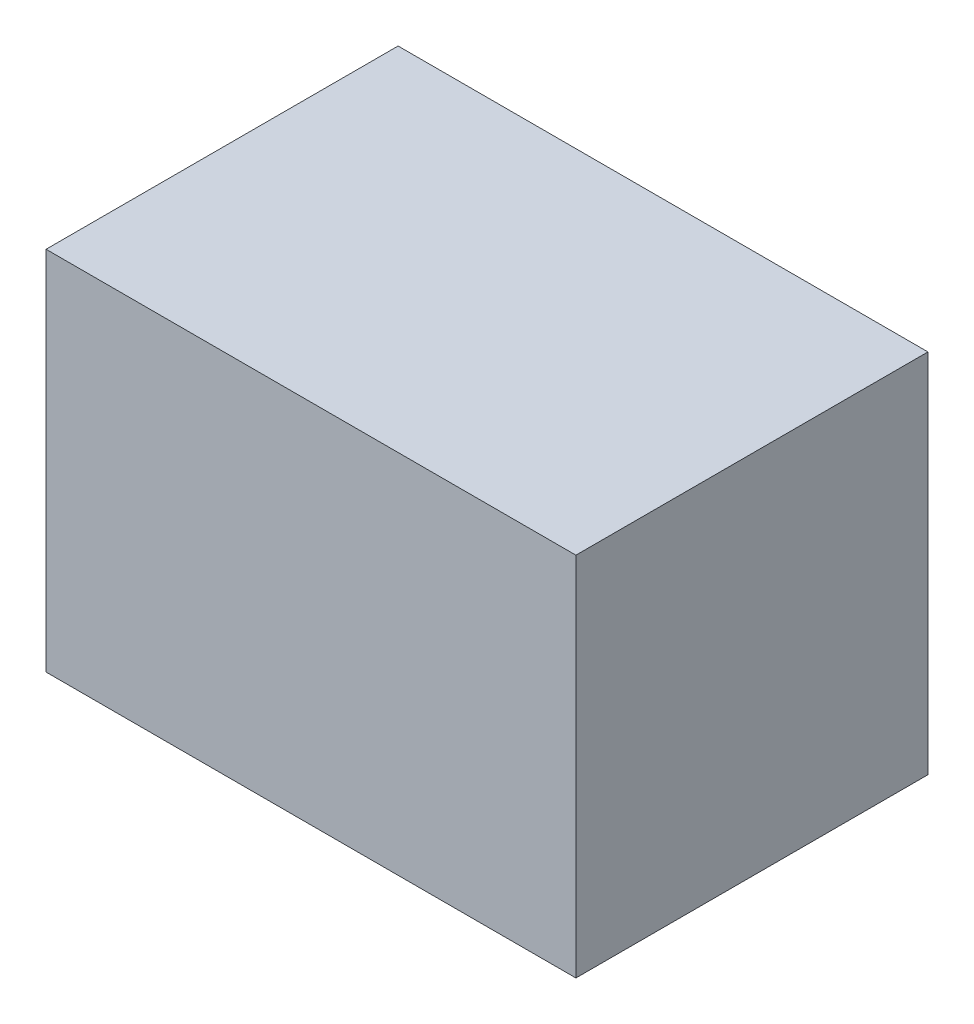
SolidWorks part; units mm, degrees
material "Nylon 6/10"
ref_plane "Front Plane" through (0, 0, 0) normal (0, 0, 1) x (1, 0, 0)
ref_plane "Top Plane" through (0, 0, 0) normal (0, 1, 0) x (1, 0, 0)
ref_plane "Right Plane" through (0, 0, 0) normal (1, 0, 0) x (0, 0, -1)
sketch "Sketch1" plane through (0, 0, 0) normal (0, 0, 1) x (1, 0, 0)
  line L1 (-45.1528, -31.206) -> (45.1528, -31.206)
  line L2 (-45.1528, -31.206) -> (-45.1528, 31.206)
  line L3 (-45.1528, 31.206) -> (45.1528, 31.206)
  line L4 (45.1528, -31.206) -> (45.1528, 31.206)
  line L5 (-45.1528, -31.206) -> (45.1528, 31.206) construction
  line L6 (-45.1528, 31.206) -> (45.1528, -31.206) construction
  point P0 (0, 0)
extrude "Boss-Extrude1" add sketch "Sketch1" along normal blind 60
